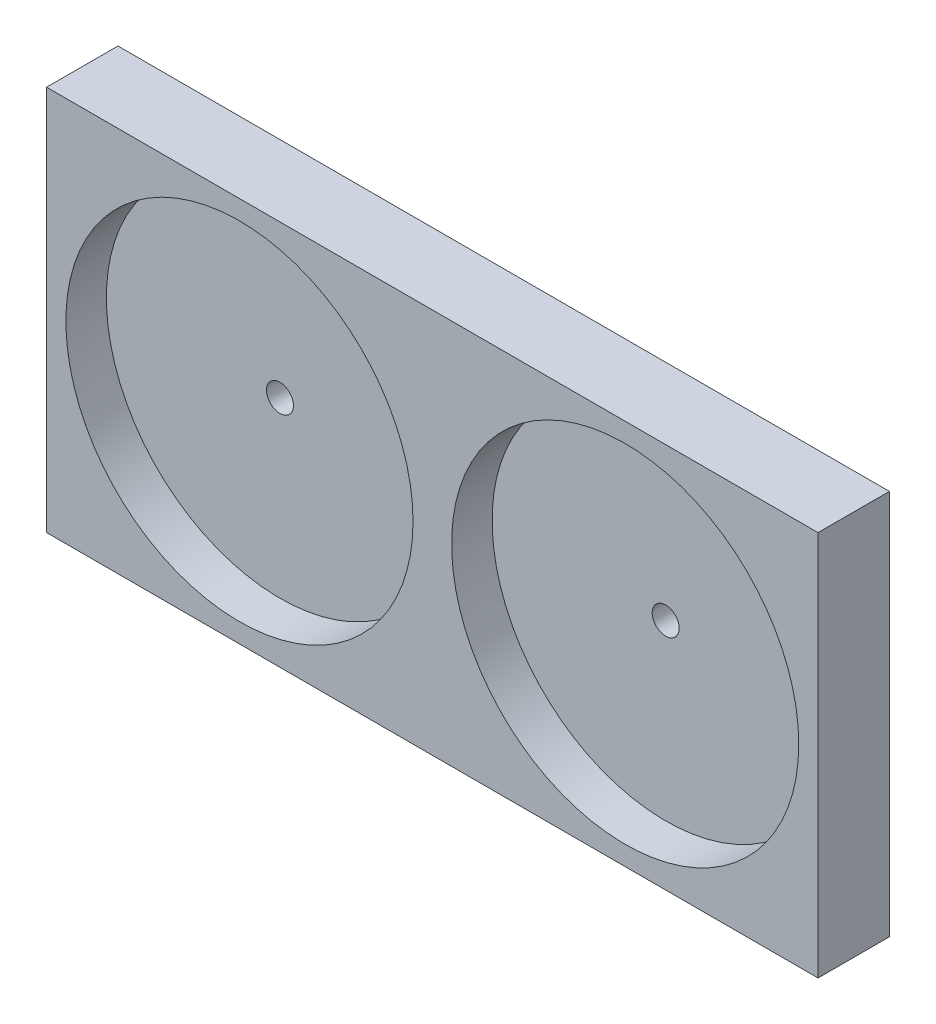
SolidWorks part; units mm, degrees
ref_plane "Front Plane" through (0, 0, 0) normal (0, 0, 1) x (1, 0, 0)
ref_plane "Top Plane" through (0, 0, 0) normal (0, 1, 0) x (1, 0, 0)
ref_plane "Right Plane" through (0, 0, 0) normal (1, 0, 0) x (0, 0, -1)
sketch "Sketch1" plane through (0, 0, 0) normal (0, 0, 1) x (1, 0, 0)
  line L1 (0, 0) -> (200, 0)
  line L2 (0, 0) -> (0, 100)
  line L3 (0, 100) -> (200, 100)
  line L4 (200, 0) -> (200, 100)
  dimension "D1" = 200
  dimension "D2" = 100
extrude "Boss-Extrude1" add sketch "Sketch1" along normal blind 18.5
sketch "Sketch2" plane through (0, 0, 18.5) normal (0, 0, 1) x (1, 0, 0)
  line L0 (0, 50) -> (200, 50) construction
  line L1 (0, 100) -> (0, 0) construction
  line L2 (200, 0) -> (200, 100) construction
  circle A0 centre (50, 50) radius 45
  circle A1 centre (150, 50) radius 45
  point P12 (100, 50)
  dimension "D1" = 90
  dimension "D2" = 90
  dimension "D3" = 50
  dimension "D4" = 50
extrude "Cut-Extrude1" cut sketch "Sketch2" against normal blind 10.5
sketch "Sketch3" plane through (0, 0, 18.5) normal (0, 0, 1) x (1, 0, 0)
  circle A0 centre (50, 50) radius 3.5
  circle A1 centre (150, 50) radius 3.5
  circle A2 centre (150, 50) radius 45 construction
  circle A4 centre (50, 50) radius 45 construction
  dimension "D1" = 7
extrude "Cut-Extrude2" cut sketch "Sketch3" against normal through all
sketch "Sketch4" plane through (0, 0, 0) normal (0, 0, -1) x (-1, 0, 0)
  line L0 (-150, 55.2961) -> (-150, 25.3943) construction
  line L1 (-133.6003, 55.2961) -> (-133.6003, 25.3943)
  line L2 (-166.3997, 55.2961) -> (-166.3997, 25.3943)
  line L3 (-50, 55.2961) -> (-50, 25.3943) construction
  line L6 (-141.6003, 55.2961) -> (-141.6003, 25.3943)
  line L7 (-158.3997, 55.2961) -> (-158.3997, 25.3943)
  line L8 (-33.6003, 55.2961) -> (-33.6003, 25.3943)
  line L9 (-66.3997, 55.2961) -> (-66.3997, 25.3943)
  line L10 (-41.6003, 55.2961) -> (-41.6003, 25.3943)
  line L13 (-58.3997, 55.2961) -> (-58.3997, 25.3943)
  arc A0 (-133.6003, 55.2961) -> (-166.3997, 55.2961) centre (-150, 55.2961) ccw
  arc A1 (-166.3997, 25.3943) -> (-133.6003, 25.3943) centre (-150, 25.3943) ccw
  arc A4 (-158.3997, 25.3943) -> (-141.6003, 25.3943) centre (-150, 25.3943) ccw
  arc A5 (-141.6003, 55.2961) -> (-158.3997, 55.2961) centre (-150, 55.2961) ccw
  arc A6 (-33.6003, 55.2961) -> (-66.3997, 55.2961) centre (-50, 55.2961) ccw
  arc A7 (-66.3997, 25.3943) -> (-33.6003, 25.3943) centre (-50, 25.3943) ccw
  circle A10 centre (-50, 50) radius 3 construction
  arc A11 (-58.3997, 25.3943) -> (-41.6003, 25.3943) centre (-50, 25.3943) ccw
  arc A12 (-41.6003, 55.2961) -> (-58.3997, 55.2961) centre (-50, 55.2961) ccw
  circle A13 centre (-50, 50) radius 3 construction
  circle A14 centre (-150, 50) radius 3 construction
  circle A15 centre (-150, 50) radius 3 construction
  point P2 (-150, 40.3452)
  point P9 (-50, 40.3452)
  dimension "D1" = 8
  dimension "D2" = 8
extrude "Cut-Extrude4" cut sketch "Sketch4" against normal blind 3
sketch "Sketch5" plane through (0, 0, 0) normal (0, 0, -1) x (-1, 0, 0)
  line L0 (-110.12, 30.25) -> (-89.8, 30.25) construction
  line L1 (-110.12, 32.25) -> (-89.8, 32.25)
  line L2 (-110.12, 28.25) -> (-89.8, 28.25)
  line L3 (-110.12, 15) -> (-89.8, 15) construction
  line L4 (-110.12, 17) -> (-89.8, 17)
  line L5 (-110.12, 13) -> (-89.8, 13)
  arc A0 (-110.12, 32.25) -> (-110.12, 28.25) centre (-110.12, 30.25) ccw
  arc A1 (-89.8, 28.25) -> (-89.8, 32.25) centre (-89.8, 30.25) ccw
  arc A2 (-110.12, 17) -> (-110.12, 13) centre (-110.12, 15) ccw
  arc A3 (-89.8, 13) -> (-89.8, 17) centre (-89.8, 15) ccw
  circle A4 centre (-110.12, 30.25) radius 0.5 construction
  circle A5 centre (-110.12, 30.25) radius 0.5 construction
  circle A6 centre (-89.8, 30.25) radius 0.5 construction
  circle A7 centre (-89.8, 30.25) radius 0.5 construction
  circle A8 centre (-89.8, 15) radius 0.5 construction
  circle A9 centre (-89.8, 15) radius 0.5 construction
  circle A10 centre (-110.12, 15) radius 0.5 construction
  circle A11 centre (-110.12, 15) radius 0.5 construction
  point P2 (-99.96, 30.25)
  point P7 (-99.96, 15)
  dimension "D1" = 4
extrude "Cut-Extrude5" cut sketch "Sketch5" against normal blind 2
